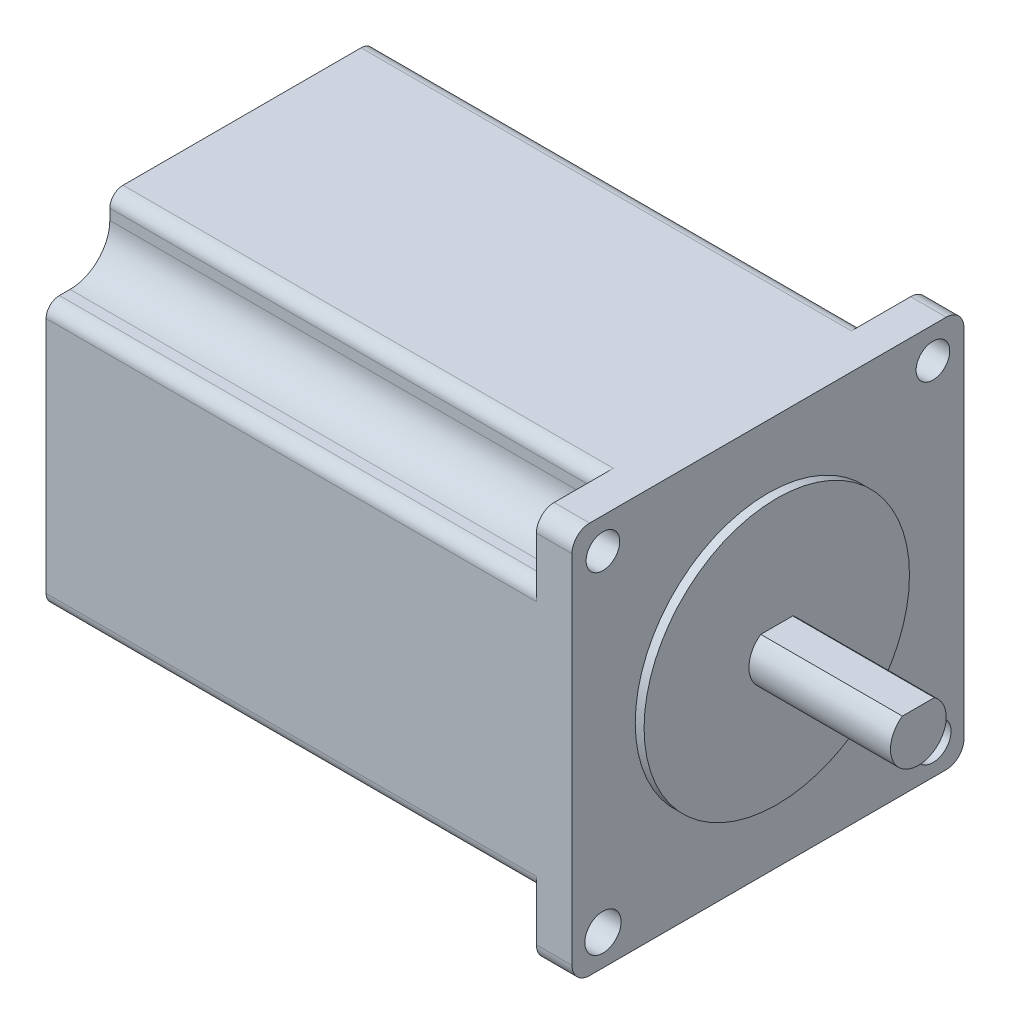
SolidWorks part; units mm, degrees
ref_plane "Front Plane" through (0, 0, 0) normal (0, 0, 1) x (1, 0, 0)
ref_plane "Top Plane" through (0, 0, 0) normal (0, 1, 0) x (1, 0, 0)
ref_plane "Right Plane" through (0, 0, 0) normal (1, 0, 0) x (0, 0, -1)
sketch "Sketch1" plane through (0, 0, 0) normal (1, 0, 0) x (0, 0, -1)
  line L1 (28.1305, -28.1305) -> (-28.1305, -28.1305)
  line L2 (28.1305, -28.1305) -> (28.1305, 28.1305)
  line L3 (28.1305, 28.1305) -> (-28.1305, 28.1305)
  line L4 (-28.1305, -28.1305) -> (-28.1305, 28.1305)
  line L5 (28.1305, -28.1305) -> (-28.1305, 28.1305) construction
  line L6 (28.1305, 28.1305) -> (-28.1305, -28.1305) construction
  point P0 (0, 0)
  dimension "D1" = 56.261
extrude "Boss-Extrude2" add sketch "Sketch1" along normal blind 75.4888 contours L3 L4 L1 L2
sketch "Sketch2" plane through (75.4888, 0, 0) normal (1, 0, 0) x (0, 0, -1)
  circle A0 centre (0, 0) radius 19.05
  dimension "D1" = 38.1
extrude "Boss-Extrude3" add sketch "Sketch2" along normal blind 1.27
sketch "Sketch3" plane through (0, 0, 0) normal (-1, 0, 0) x (0, 0, 1)
  line L0 (28.1305, 18.9865) -> (24.7015, 18.9865)
  line L1 (-28.1305, 28.1305) -> (-18.9865, 28.1305)
  line L2 (-28.1305, 28.1305) -> (-28.1305, 18.9865)
  line L3 (-28.1305, 18.9865) -> (-24.7015, 18.9865)
  line L4 (-18.9865, 28.1305) -> (-18.9865, 24.7015)
  line L5 (28.1305, 28.1305) -> (28.1305, 18.9865)
  line L6 (28.1305, 28.1305) -> (18.9865, 28.1305)
  line L7 (18.9865, 28.1305) -> (18.9865, 24.7015)
  line L8 (18.9865, -28.1305) -> (18.9865, -24.7015)
  line L9 (28.1305, -28.1305) -> (18.9865, -28.1305)
  line L10 (28.1305, -28.1305) -> (28.1305, -18.9865)
  line L11 (28.1305, -18.9865) -> (24.7015, -18.9865)
  line L12 (-28.1305, -18.9865) -> (-24.7015, -18.9865)
  line L13 (-28.1305, -28.1305) -> (-28.1305, -18.9865)
  line L14 (-28.1305, -28.1305) -> (-18.9865, -28.1305)
  line L15 (-18.9865, -28.1305) -> (-18.9865, -24.7015)
  arc A0 (-24.7015, 18.9865) -> (-18.9865, 24.7015) centre (-24.7015, 24.7015) ccw
  arc A1 (18.9865, 24.7015) -> (24.7015, 18.9865) centre (24.7015, 24.7015) ccw
  arc A2 (24.7015, -18.9865) -> (18.9865, -24.7015) centre (24.7015, -24.7015) ccw
  arc A3 (-18.9865, -24.7015) -> (-24.7015, -18.9865) centre (-24.7015, -24.7015) ccw
  point P28 (0, 0)
  dimension "D2" = 5.715
  dimension "D1" = 9.144
extrude "Cut-Extrude1" cut sketch "Sketch3" against normal blind 70.3834
fillet "Fillet1" radius 2.54 4 edges at (72.9361, -28.1305, 28.1305) (72.9361, 28.1305, 28.1305) (72.9361, -28.1305, -28.1305) (72.9361, 28.1305, -28.1305)
fillet "Fillet2" radius 1.905 8 edges at (35.1917, -28.1305, -18.9865) (35.1917, -18.9865, -28.1305) (35.1917, 18.9865, -28.1305) (35.1917, 28.1305, -18.9865) (35.1917, 28.1305, 18.9865) (35.1917, 18.9865, 28.1305) (35.1917, -18.9865, 28.1305) (35.1917, -28.1305, 18.9865)
sketch "Sketch4" plane through (70.3834, 0, 0) normal (-1, 0, 0) x (0, 0, 1)
  line L0 (-25.5905, -28.1305) -> (-17.0815, -28.1305) construction
  line L1 (-28.1305, -17.0815) -> (-28.1305, -25.5905) construction
  line L2 (28.1305, -25.5905) -> (28.1305, -17.0815) construction
  line L3 (25.5905, 28.1305) -> (17.0815, 28.1305) construction
  circle A0 centre (-23.6855, 23.6855) radius 2.413
  circle A1 centre (23.6855, 23.6855) radius 2.413
  circle A2 centre (23.6855, -23.6855) radius 2.6035
  circle A3 centre (-23.6855, -23.6855) radius 2.6035
  point P10 (0, 0)
  point P12 (0, 0)
  dimension "D1" = 4.826
  dimension "D2" = 5.207
  dimension "D3" = 4.445
  dimension "D4" = 4.445
  dimension "D5" = 4.445
  dimension "D6" = 4.445
extrude "Cut-Extrude2" cut sketch "Sketch4" against normal up to surface (5.1054 mm away) up to face at (75.4888, 0, -19.05)
sketch "Sketch5" plane through (76.7588, 0, 0) normal (1, 0, 0) x (0, 0, -1)
  line L0 (-2.2952, 3.2766) -> (2.2952, 3.2766)
  arc A0 (-2.2952, 3.2766) -> (2.2952, 3.2766) centre (0, 0) ccw
  dimension "D1" = 8.001
  dimension "D2" = 3.2766
extrude "Boss-Extrude4" add sketch "Sketch5" along normal blind 20.32
sketch "Sketch6" plane through (0, -28.1305, 0) normal (0, -1, 0) x (1, 0, 0)
  line L0 (0, 5.715) -> (0, -5.715)
  line L1 (0, -17.0815) -> (0, 17.0815) construction
  line L2 (0, 5.715) -> (11.049, 5.715)
  line L3 (11.049, 5.715) -> (11.049, -5.715)
  line L4 (11.049, -5.715) -> (0, -5.715)
  circle A0 centre (6.858, 0) radius 2.8575
  point P6 (0, 0)
  dimension "D3" = 5.715
  dimension "D1" = 11.43
  dimension "D2" = 11.049
  dimension "D4" = 6.858
extrude "Boss-Extrude5" add sketch "Sketch6" along normal blind 1.524
sketch "Sketch7" plane through (0, -28.1305, 0) normal (0, -1, 0) x (1, 0, 0)
  circle A0 centre (6.858, 1.2855) radius 0.8255
  circle A1 centre (6.858, 0) radius 2.8575 construction
  circle A2 centre (8.1435, 0) radius 0.8255
  circle A3 centre (6.858, 0) radius 2.8575 construction
  circle A4 centre (6.858, -1.2855) radius 0.8255
  circle A5 centre (6.858, 0) radius 2.8575 construction
  circle A6 centre (5.5725, 0) radius 0.8255
  circle A7 centre (6.858, 0) radius 2.8575 construction
  point P17 (6.858, 0)
  dimension "D1" = 1.651
extrude "Boss-Extrude6" add sketch "Sketch7" along normal blind 12.7
